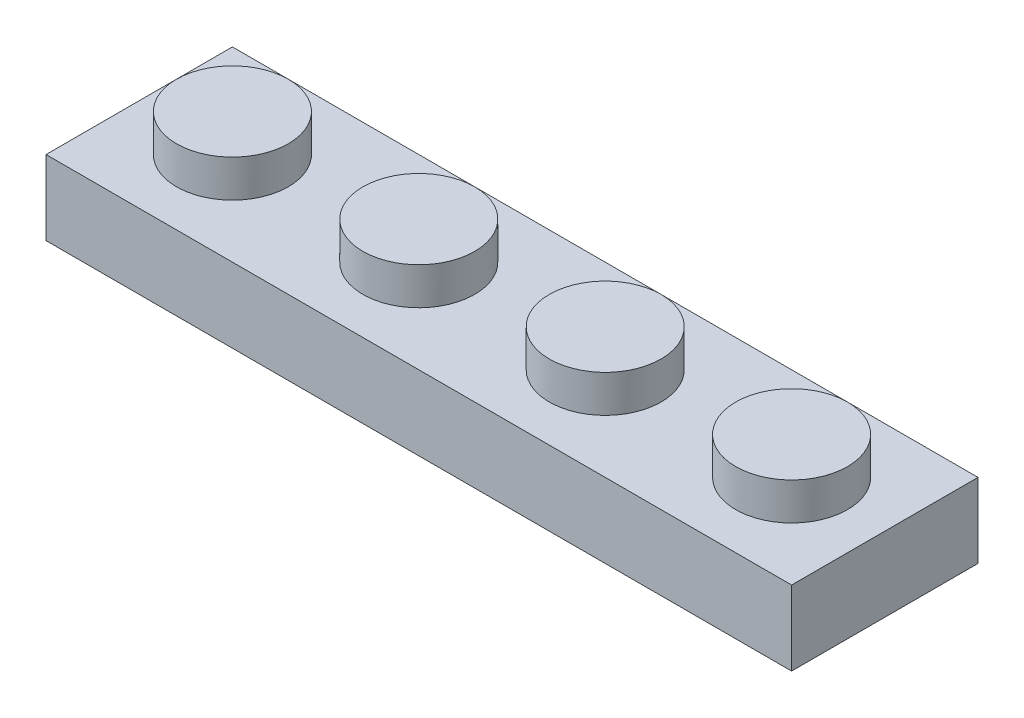
SolidWorks part; units mm, degrees
ref_plane "Front Plane" through (0, 0, 0) normal (0, 0, 1) x (1, 0, 0)
ref_plane "Top Plane" through (0, 0, 0) normal (0, 1, 0) x (1, 0, 0)
ref_plane "Right Plane" through (0, 0, 0) normal (1, 0, 0) x (0, 0, -1)
sketch "Sketch1" plane through (0, 0, 0) normal (0, 1, 0) x (1, 0, 0)
  line L1 (0, 0) -> (31.75, 0)
  line L2 (0, 0) -> (0, 7.9375)
  line L3 (0, 7.9375) -> (31.75, 7.9375)
  line L4 (31.75, 0) -> (31.75, 7.9375)
  dimension "D1" = 31.75
  dimension "D2" = 7.9375
extrude "Boss-Extrude1" add sketch "Sketch1" along normal blind 3.175
sketch "Sketch2" plane through (0, 3.175, 0) normal (0, 1, 0) x (1, 0, 0)
  circle A0 centre (3.9688, 3.9688) radius 2.3813
  circle A1 centre (11.9062, 3.9688) radius 2.3813
  circle A2 centre (19.8438, 3.9688) radius 2.3813
  circle A3 centre (27.7812, 3.9688) radius 2.3813
  dimension "D2" = 4.7625
  dimension "D4" = 4.7625
  dimension "D6" = 4.7625
  dimension "D8" = 4.7625
  dimension "D3" = 7.9375
  dimension "D5" = 7.9375
  dimension "D7" = 7.9375
extrude "Boss-Extrude2" add sketch "Sketch2" along normal blind 1.5875
shell "Shell1" thickness 1.5875
sketch "Sketch3" plane through (0, 1.5875, 0) normal (0, -1, 0) x (1, 0, 0)
  circle A0 centre (7.5406, -3.9688) radius 1.5875
  circle A1 centre (15.4781, -3.9688) radius 1.5875
  circle A2 centre (23.4156, -3.9688) radius 1.5875
  circle A3 centre (7.5406, -3.9688) radius 0.7938
  circle A4 centre (15.4781, -3.9688) radius 0.7938
  circle A5 centre (23.4156, -3.9688) radius 0.7937
  dimension "D2" = 3.175
  dimension "D4" = 3.175
  dimension "D6" = 3.175
  dimension "D1" = 0.7937
extrude "Boss-Extrude4" add sketch "Sketch3" along normal blind 1.397
